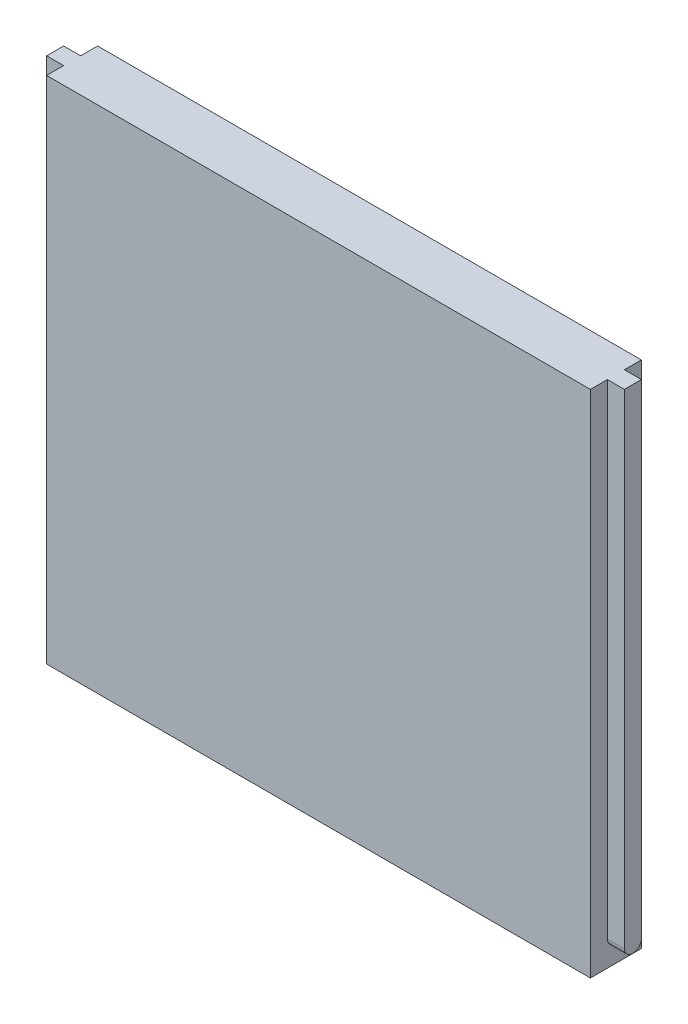
SolidWorks part; units mm, degrees
material "Acrylic (Medium-high impact)"
ref_plane "Front Plane" through (0, 0, 0) normal (0, 0, 1) x (1, 0, 0)
ref_plane "Top Plane" through (0, 0, 0) normal (0, 1, 0) x (1, 0, 0)
ref_plane "Right Plane" through (0, 0, 0) normal (1, 0, 0) x (0, 0, -1)
sketch "Sketch1" plane through (0, 0, 0) normal (0, 0, 1) x (1, 0, 0)
  line L0 (-80, 83.7549) -> (80, 83.7549)
  line L1 (80, 83.7549) -> (80, -66.2451)
  line L2 (80, -66.2451) -> (-80, -66.2451)
  line L3 (-80, -66.2451) -> (-80, 83.7549)
  dimension "D1" = 160
  dimension "D2" = 150
  dimension "D3" = 80
extrude "Boss-Extrude1" add sketch "Sketch1" along normal blind 15
sketch "Sketch2" plane through (80, 0, 0) normal (1, 0, 0) x (0, 0, -1)
  line L0 (-7.5, -58.7451) -> (-7.5, 89.5202) construction
  line L1 (-10, -58.7451) -> (-10, 89.5202)
  line L2 (-5, -58.7451) -> (-5, 89.5202)
  line L3 (0, -66.2451) -> (0, 83.7549) construction
  line L4 (-15, -66.2451) -> (0, -66.2451) construction
  arc A0 (-10, -58.7451) -> (-5, -58.7451) centre (-7.5, -58.7451) ccw
  arc A1 (-5, 89.5202) -> (-10, 89.5202) centre (-7.5, 89.5202) ccw
  point P2 (-7.5, 15.3875)
  dimension "D1" = 5
  dimension "D2" = 5
  dimension "D3" = 7.5
extrude "Boss-Extrude2" add sketch "Sketch2" along normal blind 5
mirror "Mirror1" about plane through (0, 0, 0) normal (1, 0, 0) of "Boss-Extrude2"
sketch "Sketch3" plane through (-85, 0, 0) normal (-1, 0, 0) x (0, 0, 1)
  line L0 (5, 83.7549) -> (10, 83.7549)
  line L1 (10, 83.7549) -> (10, 89.5202)
  line L3 (5, 89.5202) -> (5, 83.7549)
  arc A0 (10, 89.5202) -> (5, 89.5202) centre (7.5, 89.5202) ccw
extrude "Cut-Extrude1" cut sketch "Sketch3" against normal blind 5
mirror "Mirror2" about plane through (0, 0, 0) normal (1, 0, 0) of "Cut-Extrude1"
